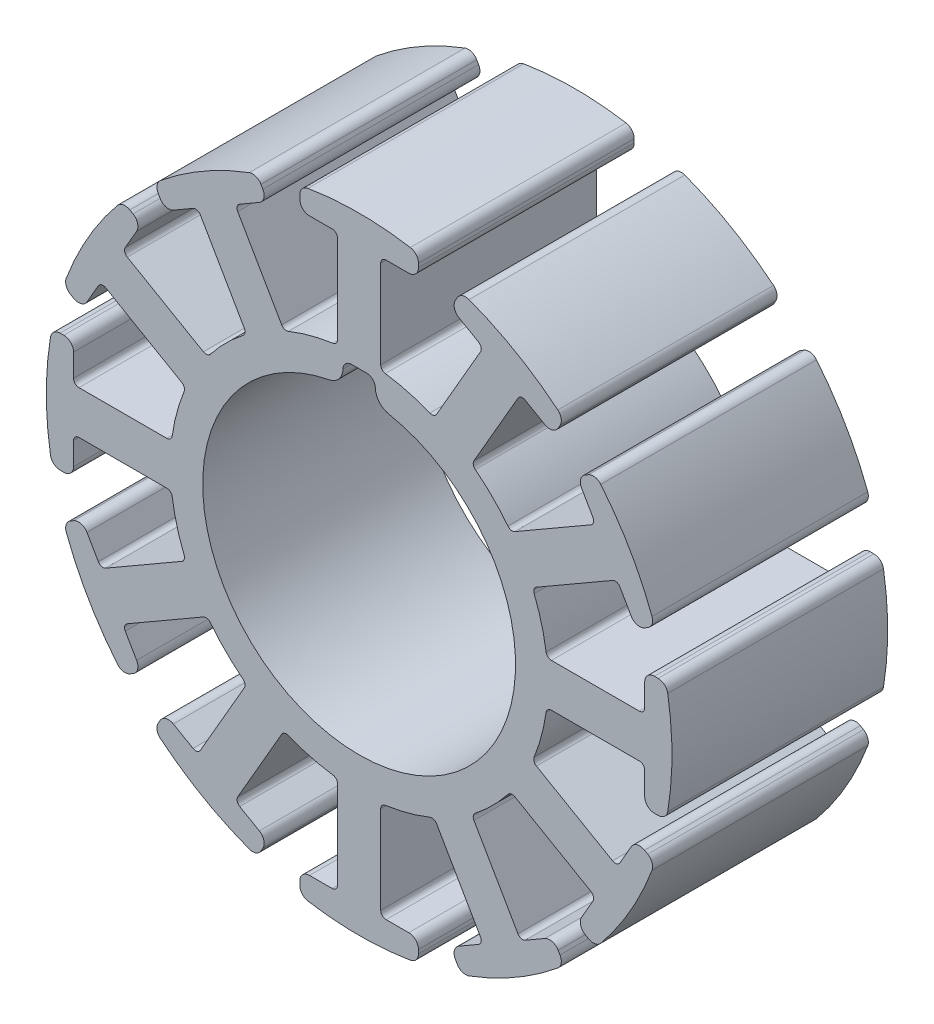
SolidWorks part; units mm, degrees
material "AISI 347 軟ｽﾃﾝﾚｽ鋼 (SS)"
ref_plane "正面" through (0, 0, 0) normal (0, 0, 1) x (1, 0, 0)
ref_plane "平面" through (0, 0, 0) normal (0, 1, 0) x (1, 0, 0)
ref_plane "右側面" through (0, 0, 0) normal (1, 0, 0) x (0, 0, -1)
sketch "ｽｹｯﾁ1" plane through (0, 0, 0) normal (0, 0, 1) x (1, 0, 0)
  line L0 (0, 29) -> (0, 0) construction
  line L1 (-5.5, 28.4737) -> (5.5, 28.4737) construction
  line L2 (-2, 26.4737) -> (-2, 17.3853)
  line L3 (2, 26.4737) -> (2, 17.3853)
  line L4 (14.9689, 21.9269) -> (10.4247, 14.0561)
  line L5 (18, 20.1769) -> (14.9689, 21.9269)
  line L6 (-5.5, 28.4737) -> (-5.5, 26.4737)
  line L7 (-5.5, 26.4737) -> (-2, 26.4737)
  line L8 (5.5, 28.4737) -> (5.5, 26.4737)
  line L9 (5.5, 26.4737) -> (2, 26.4737)
  line L10 (19, 21.9089) -> (18, 20.1769)
  line L11 (9.4737, 27.4089) -> (8.4737, 25.6769)
  line L12 (8.4737, 25.6769) -> (11.5048, 23.9269)
  line L13 (11.5048, 23.9269) -> (6.9606, 16.0561)
  line L14 (23.9269, 11.5048) -> (16.0561, 6.9606)
  line L15 (25.6769, 8.4737) -> (23.9269, 11.5048)
  line L16 (27.4089, 9.4737) -> (25.6769, 8.4737)
  line L17 (21.9089, 19) -> (20.1769, 18)
  line L18 (20.1769, 18) -> (21.9269, 14.9689)
  line L19 (21.9269, 14.9689) -> (14.0561, 10.4247)
  line L20 (26.4737, -2) -> (17.3853, -2)
  line L21 (26.4737, -5.5) -> (26.4737, -2)
  line L22 (28.4737, -5.5) -> (26.4737, -5.5)
  line L23 (28.4737, 5.5) -> (26.4737, 5.5)
  line L24 (26.4737, 5.5) -> (26.4737, 2)
  line L25 (26.4737, 2) -> (17.3853, 2)
  line L26 (21.9269, -14.9689) -> (14.0561, -10.4247)
  line L27 (20.1769, -18) -> (21.9269, -14.9689)
  line L28 (21.9089, -19) -> (20.1769, -18)
  line L29 (27.4089, -9.4737) -> (25.6769, -8.4737)
  line L30 (25.6769, -8.4737) -> (23.9269, -11.5048)
  line L31 (23.9269, -11.5048) -> (16.0561, -6.9606)
  line L32 (11.5048, -23.9269) -> (6.9606, -16.0561)
  line L33 (8.4737, -25.6769) -> (11.5048, -23.9269)
  line L34 (9.4737, -27.4089) -> (8.4737, -25.6769)
  line L35 (19, -21.9089) -> (18, -20.1769)
  line L36 (18, -20.1769) -> (14.9689, -21.9269)
  line L37 (14.9689, -21.9269) -> (10.4247, -14.0561)
  line L38 (-2, -26.4737) -> (-2, -17.3853)
  line L39 (-5.5, -26.4737) -> (-2, -26.4737)
  line L40 (-5.5, -28.4737) -> (-5.5, -26.4737)
  line L41 (5.5, -28.4737) -> (5.5, -26.4737)
  line L42 (5.5, -26.4737) -> (2, -26.4737)
  line L43 (2, -26.4737) -> (2, -17.3853)
  line L44 (-14.9689, -21.9269) -> (-10.4247, -14.0561)
  line L45 (-18, -20.1769) -> (-14.9689, -21.9269)
  line L46 (-19, -21.9089) -> (-18, -20.1769)
  line L47 (-9.4737, -27.4089) -> (-8.4737, -25.6769)
  line L48 (-8.4737, -25.6769) -> (-11.5048, -23.9269)
  line L49 (-11.5048, -23.9269) -> (-6.9606, -16.0561)
  line L50 (-23.9269, -11.5048) -> (-16.0561, -6.9606)
  line L51 (-25.6769, -8.4737) -> (-23.9269, -11.5048)
  line L52 (-27.4089, -9.4737) -> (-25.6769, -8.4737)
  line L53 (-21.9089, -19) -> (-20.1769, -18)
  line L54 (-20.1769, -18) -> (-21.9269, -14.9689)
  line L55 (-21.9269, -14.9689) -> (-14.0561, -10.4247)
  line L56 (-26.4737, 2) -> (-17.3853, 2)
  line L57 (-26.4737, 5.5) -> (-26.4737, 2)
  line L58 (-28.4737, 5.5) -> (-26.4737, 5.5)
  line L59 (-28.4737, -5.5) -> (-26.4737, -5.5)
  line L60 (-26.4737, -5.5) -> (-26.4737, -2)
  line L61 (-26.4737, -2) -> (-17.3853, -2)
  line L62 (-21.9269, 14.9689) -> (-14.0561, 10.4247)
  line L63 (-20.1769, 18) -> (-21.9269, 14.9689)
  line L64 (-21.9089, 19) -> (-20.1769, 18)
  line L65 (-27.4089, 9.4737) -> (-25.6769, 8.4737)
  line L66 (-25.6769, 8.4737) -> (-23.9269, 11.5048)
  line L67 (-23.9269, 11.5048) -> (-16.0561, 6.9606)
  line L68 (-11.5048, 23.9269) -> (-6.9606, 16.0561)
  line L69 (-8.4737, 25.6769) -> (-11.5048, 23.9269)
  line L70 (-9.4737, 27.4089) -> (-8.4737, 25.6769)
  line L71 (-19, 21.9089) -> (-18, 20.1769)
  line L72 (-18, 20.1769) -> (-14.9689, 21.9269)
  line L73 (-14.9689, 21.9269) -> (-10.4247, 14.0561)
  circle A0 centre (0, 0) radius 29 construction
  arc A1 (-2, 17.3853) -> (-6.9606, 16.0561) centre (0, 0) ccw
  circle A2 centre (0, 0) radius 14.5
  arc A3 (-5.5, 28.4737) -> (5.5, 28.4737) centre (0, 0) cw
  arc A4 (9.4737, 27.4089) -> (19, 21.9089) centre (0, 0) cw
  arc A5 (21.9089, 19) -> (27.4089, 9.4737) centre (0, 0) cw
  arc A6 (28.4737, 5.5) -> (28.4737, -5.5) centre (0, 0) cw
  arc A7 (27.4089, -9.4737) -> (21.9089, -19) centre (0, 0) cw
  arc A8 (19, -21.9089) -> (9.4737, -27.4089) centre (0, 0) cw
  arc A9 (5.5, -28.4737) -> (-5.5, -28.4737) centre (0, 0) cw
  arc A10 (-9.4737, -27.4089) -> (-19, -21.9089) centre (0, 0) cw
  arc A11 (-21.9089, -19) -> (-27.4089, -9.4737) centre (0, 0) cw
  arc A12 (-28.4737, -5.5) -> (-28.4737, 5.5) centre (0, 0) cw
  arc A13 (-27.4089, 9.4737) -> (-21.9089, 19) centre (0, 0) cw
  arc A14 (-19, 21.9089) -> (-9.4737, 27.4089) centre (0, 0) cw
  arc A15 (6.9606, 16.0561) -> (2, 17.3853) centre (0, 0) ccw
  arc A16 (14.0561, 10.4247) -> (10.4247, 14.0561) centre (0, 0) ccw
  arc A17 (17.3853, 2) -> (16.0561, 6.9606) centre (0, 0) ccw
  arc A18 (16.0561, -6.9606) -> (17.3853, -2) centre (0, 0) ccw
  arc A19 (10.4247, -14.0561) -> (14.0561, -10.4247) centre (0, 0) ccw
  arc A20 (2, -17.3853) -> (6.9606, -16.0561) centre (0, 0) ccw
  arc A21 (-6.9606, -16.0561) -> (-2, -17.3853) centre (0, 0) ccw
  arc A22 (-14.0561, -10.4247) -> (-10.4247, -14.0561) centre (0, 0) ccw
  arc A23 (-17.3853, -2) -> (-16.0561, -6.9606) centre (0, 0) ccw
  arc A24 (-16.0561, 6.9606) -> (-17.3853, 2) centre (0, 0) ccw
  arc A25 (-10.4247, 14.0561) -> (-14.0561, 10.4247) centre (0, 0) ccw
  point P105 (0, 0)
  dimension "D1" = 58
  dimension "D4" = 29
  dimension "D5" = 35
  dimension "D2" = 2
  dimension "D3" = 2
  dimension "D6" = 11
  dimension "D7" = 2
  dimension "D8" = 12
extrude "ﾎﾞｽ - 押し出し1" add sketch "ｽｹｯﾁ1" along normal blind 20
fillet "ﾌｨﾚｯﾄ1" radius 0.9 4 edges at (-18, 20.1769, 10) (-19, 21.9089, 10) (-9.4737, 27.4089, 10) (-8.4737, 25.6769, 10)
fillet "ﾌｨﾚｯﾄ2" radius 0.9 12 edges at (25.6769, 8.4737, 10) (18, 20.1769, 10) (20.1769, 18, 10) (27.4089, 9.4737, 10) (5.5, 26.4737, 10) (21.9089, 19, 10) (19, 21.9089, 10) (8.4737, 25.6769, 10) (9.4737, 27.4089, 10) (5.5, 28.4737, 10) (-5.5, 26.4737, 10) (-5.5, 28.4737, 10)
fillet "ﾌｨﾚｯﾄ3" radius 0.9 8 edges at (21.9089, -19, 10) (20.1769, -18, 10) (27.4089, -9.4737, 10) (25.6769, -8.4737, 10) (26.4737, 5.5, 10) (26.4737, -5.5, 10) (28.4737, -5.5, 10) (28.4737, 5.5, 10)
fillet "ﾌｨﾚｯﾄ4" radius 0.9 24 edges at (-21.9089, 19, 10) (-20.1769, 18, 10) (-27.4089, 9.4737, 10) (-25.6769, 8.4737, 10) (-26.4737, 5.5, 10) (-28.4737, 5.5, 10) (-26.4737, -5.5, 10) (-28.4737, -5.5, 10) (-25.6769, -8.4737, 10) (-27.4089, -9.4737, 10) (-21.9089, -19, 10) (-20.1769, -18, 10) (-18, -20.1769, 10) (-19, -21.9089, 10) (-9.4737, -27.4089, 10) (-8.4737, -25.6769, 10) (-5.5, -26.4737, 10) (-5.5, -28.4737, 10) (5.5, -26.4737, 10) (5.5, -28.4737, 10) (9.4737, -27.4089, 10) (8.4737, -25.6769, 10) (19, -21.9089, 10) (18, -20.1769, 10)
fillet "ﾌｨﾚｯﾄ5" radius 0.5 26 edges at (-23.9269, -11.5048, 10) (-16.0561, -6.9606, 10) (-21.9269, -14.9689, 10) (-14.0561, -10.4247, 10) (-14.9689, -21.9269, 10) (-10.4247, -14.0561, 10) (-11.5048, -23.9269, 10) (-6.9606, -16.0561, 10) (-2, -26.4737, 10) (-2, -17.3853, 10) (2, -26.4737, 10) (2, -17.3853, 10) (6.9606, -16.0561, 10) (11.5048, -23.9269, 10) (14.9689, -21.9269, 10) (10.4247, -14.0561, 10) (21.9269, -14.9689, 10) (14.0561, -10.4247, 10) (23.9269, -11.5048, 10) (16.0561, -6.9606, 10) (17.3853, -2, 10) (26.4737, -2, 10) (26.4737, 2, 10) (17.3853, 2, 10) (16.0561, 6.9606, 10) (23.9269, 11.5048, 10)
fillet "ﾌｨﾚｯﾄ6" radius 0.5 22 edges at (21.9269, 14.9689, 10) (14.0561, 10.4247, 10) (10.4247, 14.0561, 10) (14.9689, 21.9269, 10) (11.5048, 23.9269, 10) (6.9606, 16.0561, 10) (-2, 17.3853, 10) (-2, 26.4737, 10) (2, 26.4737, 10) (-11.5048, 23.9269, 10) (-10.4247, 14.0561, 10) (-21.9269, 14.9689, 10) (-14.9689, 21.9269, 10) (-23.9269, 11.5048, 10) (-16.0561, 6.9606, 10) (2, 17.3853, 10) (-6.9606, 16.0561, 10) (-14.0561, 10.4247, 10) (-26.4737, 2, 10) (-17.3853, 2, 10) (-26.4737, -2, 10) (-17.3853, -2, 10)
sketch "ｽｹｯﾁ3" plane through (0, 0, 20) normal (0, 0, 1) x (1, 0, 0)
  line L1 (-1.5, 12.5) -> (1.5, 12.5)
  line L2 (-1.5, 12.5) -> (-1.5, 16.5)
  line L3 (-1.5, 16.5) -> (1.5, 16.5)
  line L4 (1.5, 12.5) -> (1.5, 16.5)
  line L5 (-1.5, 12.5) -> (1.5, 16.5) construction
  line L6 (-1.5, 16.5) -> (1.5, 12.5) construction
  circle A0 centre (0, 0) radius 14.5 construction
  point P0 (0, 14.5)
  dimension "D1" = 3
  dimension "D2" = 2
extrude "ｶｯﾄ - 押し出し1" cut sketch "ｽｹｯﾁ3" against normal through all
fillet "ﾌｨﾚｯﾄ7" radius 1.55 2 edges at (1.5, 14.4222, 10) (-1.5, 14.4222, 10)
fillet "ﾌｨﾚｯﾄ8" radius 0.8 2 edges at (1.5, 16.5, 10) (-1.5, 16.5, 10)
